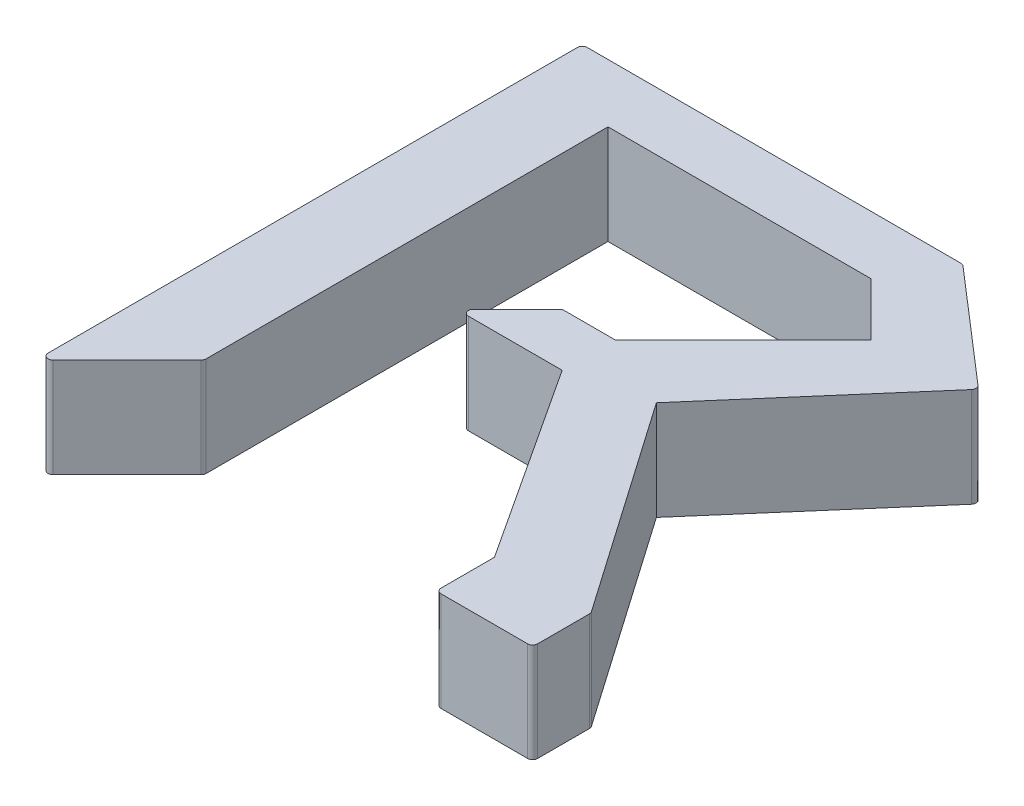
SolidWorks part; units mm, degrees
ref_plane "Front Plane" through (0, 0, 0) normal (0, 0, 1) x (1, 0, 0)
ref_plane "Top Plane" through (0, 0, 0) normal (0, 1, 0) x (1, 0, 0)
ref_plane "Right Plane" through (0, 0, 0) normal (1, 0, 0) x (0, 0, -1)
sketch "Sketch2" plane through (0, 0, 0) normal (0, 1, 0) x (1, 0, 0)
  line L0 (0, 0) -> (8.4615, 8.4615)
  line L1 (40.2791, 0) -> (50, 0)
  line L2 (0, 0) -> (0, 55)
  line L3 (0, 55) -> (38.312, 55)
  line L4 (50, 0) -> (50, 5.8761)
  line L5 (8.4615, 8.4615) -> (8.4615, 49.1239)
  line L6 (38.312, 55) -> (50, 44.8932)
  line L7 (50, 44.8932) -> (34.9598, 27.5)
  line L8 (34.9598, 27.5) -> (50, 5.8761)
  line L9 (8.4615, 49.1239) -> (34.9598, 49.1239)
  line L10 (34.9598, 49.1239) -> (40.2791, 43.8047)
  line L11 (40.2791, 43.8047) -> (27.3825, 30.9081)
  line L12 (27.3825, 30.9081) -> (22.0633, 30.9081)
  line L14 (16.744, 25.5889) -> (27.3825, 25.5889)
  line L15 (27.3825, 25.5889) -> (40.2791, 5.8761)
  line L16 (40.2791, 5.8761) -> (40.2791, 0)
  line L17 (16.744, 25.5889) -> (22.0633, 30.9081)
  dimension "D1" = 55
  dimension "D2" = 50
extrude "Boss-Extrude1" add sketch "Sketch2" along normal blind 10
fillet "Fillet1" radius 0.5 10 edges at (40.2791, 5, 0) (22.0633, 5, -30.9081) (16.744, 5, -25.5889) (8.4615, 5, -8.4615) (0, 5, 0) (0, 5, -55) (38.312, 5, -55) (50, 5, 0) (50, 5, -5.8761) (50, 5, -44.8932)
